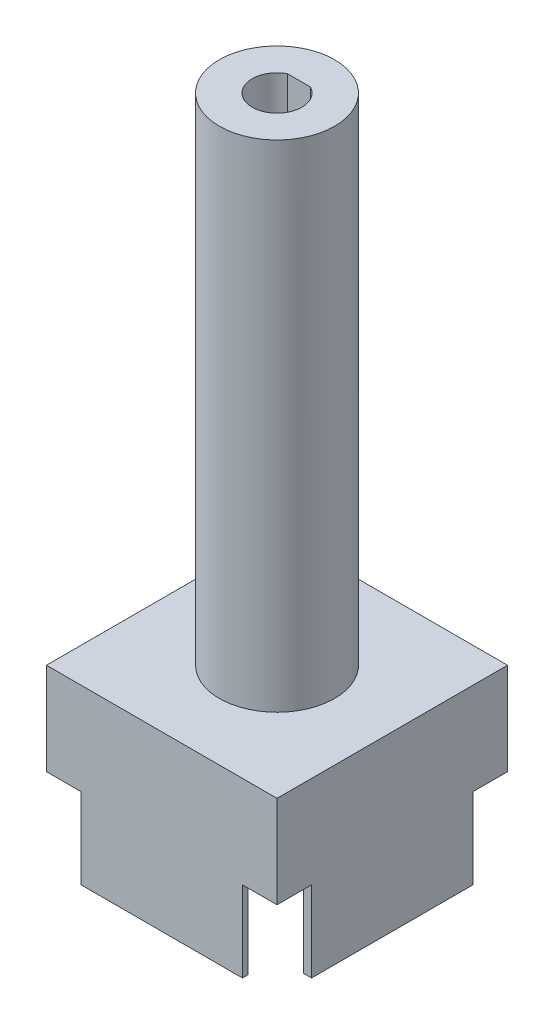
SolidWorks part; units mm, degrees
ref_plane "前基準面" through (0, 0, 0) normal (0, 0, 1) x (1, 0, 0)
ref_plane "上基準面" through (0, 0, 0) normal (0, 1, 0) x (1, 0, 0)
ref_plane "右基準面" through (0, 0, 0) normal (1, 0, 0) x (0, 0, -1)
sketch "草圖1" plane through (0, 0, 0) normal (0, 1, 0) x (1, 0, 0)
  line L1 (0, 0) -> (20, 0)
  line L2 (0, 0) -> (0, 20)
  line L3 (0, 20) -> (20, 20)
  line L4 (20, 0) -> (20, 20)
  line L5 (0.5, 0.5) -> (19.3, 0.5)
  line L6 (0.5, 0.5) -> (0.5, 19.5)
  line L7 (0.5, 19.5) -> (19.3, 19.5)
  line L8 (19.3, 0.5) -> (19.3, 19.5)
  dimension "D1" = 20
  dimension "D2" = 20
  dimension "D3" = 19
  dimension "D4" = 18.8
  dimension "D5" = 0.5
  dimension "D6" = 0.5
extrude "填料-伸長1" add sketch "草圖1" along normal blind 7
ref_plane "平面1" through (0, 7, 0) normal (0, 1, 0) x (1, 0, 0)
sketch "草圖3" plane through (0, 7, 0) normal (0, 1, 0) x (1, 0, 0)
  line L1 (0, 0) -> (20, 0)
  line L2 (0, 0) -> (0, 20)
  line L3 (0, 20) -> (20, 20)
  line L4 (20, 0) -> (20, 20)
extrude "填料-伸長2" add sketch "草圖3" along normal blind 8
sketch "草圖4" plane through (0, 15, 0) normal (0, 1, 0) x (1, 0, 0)
  line L0 (20, 0) -> (20, 20) construction
  line L1 (20, 20) -> (0, 20) construction
  circle A0 centre (10, 10) radius 5
  dimension "D1" = 10
  dimension "D2" = 10
  dimension "D3" = 10
extrude "填料-伸長3" add sketch "草圖4" along normal blind 43
sketch "草圖5" plane through (0, 58, 0) normal (0, 1, 0) x (1, 0, 0)
  line L0 (10, 10) -> (10, 11.9)
  line L1 (8, 11.9) -> (12, 11.9)
  circle A0 centre (10, 10) radius 2.15
  point P6 (10, 11.9)
  dimension "D3" = 4.3
  dimension "D1" = 1.9
  dimension "D2" = 4
extrude "除料-伸長1" cut sketch "草圖5" against normal blind 18
ref_plane "平面2" through (0, 7, 0) normal (0, 1, 0) x (1, 0, 0)
sketch "草圖6" plane through (0, 7, 0) normal (0, 1, 0) x (1, 0, 0)
  line L1 (0, 20) -> (3, 20)
  line L2 (0, 20) -> (0, 17)
  line L3 (0, 17) -> (3, 17)
  line L4 (3, 20) -> (3, 17)
  line L5 (20, 20) -> (17, 20)
  line L6 (20, 20) -> (20, 17)
  line L7 (20, 17) -> (17, 17)
  line L8 (17, 20) -> (17, 17)
  line L9 (20, 0) -> (17, 0)
  line L10 (20, 0) -> (20, 3)
  line L11 (20, 3) -> (17, 3)
  line L12 (17, 0) -> (17, 3)
  line L13 (0, 0) -> (3, 0)
  line L14 (0, 0) -> (0, 3)
  line L15 (0, 3) -> (3, 3)
  line L16 (3, 0) -> (3, 3)
  dimension "D1" = 3
  dimension "D2" = 3
  dimension "D3" = 3
  dimension "D4" = 3
  dimension "D5" = 3
extrude "除料-伸長2" cut sketch "草圖6" against normal blind 10
